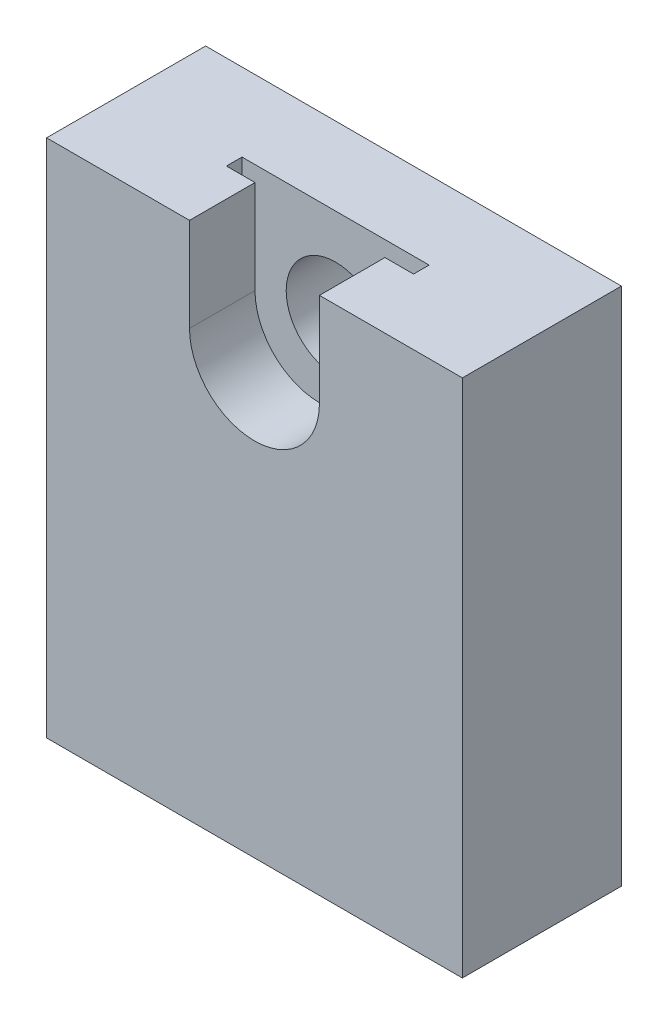
SolidWorks part; units mm, degrees
ref_plane "Front" through (0, 0, 0) normal (0, 0, 1) x (1, 0, 0)
ref_plane "Top" through (0, 0, 0) normal (0, 1, 0) x (1, 0, 0)
ref_plane "Right" through (0, 0, 0) normal (1, 0, 0) x (0, 0, -1)
sketch "Sketch2" plane through (0, 0, 0) normal (0, 0, 1) x (1, 0, 0)
  line L0 (-20, 9) -> (-20, -41)
  line L1 (-20, -41) -> (20, -41)
  line L2 (20, -41) -> (20, 9)
  line L3 (20, 9) -> (6.25, 9)
  line L4 (6.25, 9) -> (6.25, 0)
  line L5 (-6.25, 0) -> (-6.25, 9)
  line L6 (-6.25, 9) -> (-20, 9)
  arc A0 (6.25, 0) -> (-6.25, 0) centre (0, 0) cw
  point P9 (0, 0)
  dimension "D1" = 6.25
  dimension "D2" = 9
  dimension "D3" = 41
  dimension "D4" = 40
extrude "Boss-Extrude1" add sketch "Sketch2" against normal blind 15.3
sketch "Sketch3" plane through (0, 0, -15.3) normal (0, 0, -1) x (-1, 0, 0)
  line L0 (6.25, 0) -> (6.25, 9) construction
  line L1 (-6.25, 9) -> (-6.25, 0) construction
  line L2 (6.25, 0) -> (6.25, 9)
  line L3 (-6.25, 9) -> (-6.25, 0)
  line L4 (-6.25, 9) -> (6.25, 9)
  arc A0 (-6.25, 0) -> (6.25, 0) centre (0, 0) ccw construction
  arc A1 (-6.25, 0) -> (6.25, 0) centre (0, 0) ccw
  circle A2 centre (0, 0) radius 4.75
  dimension "D1" = 9.5
extrude "Boss-Extrude2" add sketch "Sketch3" against normal blind 9
sketch "Sketch4" plane through (0, 0, -6.3) normal (0, 0, 1) x (1, 0, 0)
  line L0 (0, 0) -> (0, 9) construction
  line L1 (-6.25, 9) -> (6.25, 9) construction
  line L2 (-9, 0) -> (-9, 9)
  line L3 (9, 0) -> (9, 9)
  arc A0 (-9, 0) -> (9, 0) centre (0, 0) ccw
  arc A1 (9, 9) -> (-9, 9) centre (0, 9) ccw
  point P5 (0, 4.5)
  dimension "D1" = 18
extrude "Cut-Extrude1" cut sketch "Sketch4" against normal blind 1.5
sketch "Sketch6" plane through (0, 0, -15.3) normal (0, 0, -1) x (-1, 0, 0)
  line L0 (20, 9) -> (20, -41) construction
  line L1 (-20, -8.7312) -> (20, -8.7312)
  line L2 (-20, -8.7312) -> (-20, 8.7312)
  line L3 (-20, 8.7312) -> (20, 8.7312)
  line L4 (20, -8.7312) -> (20, 8.7312)
  line L5 (0, 8.7312) -> (0, -8.7312) construction
  line L6 (-20, 0) -> (20, 0) construction
  point P0 (0, 0)
  dimension "D1" = 17.4625
